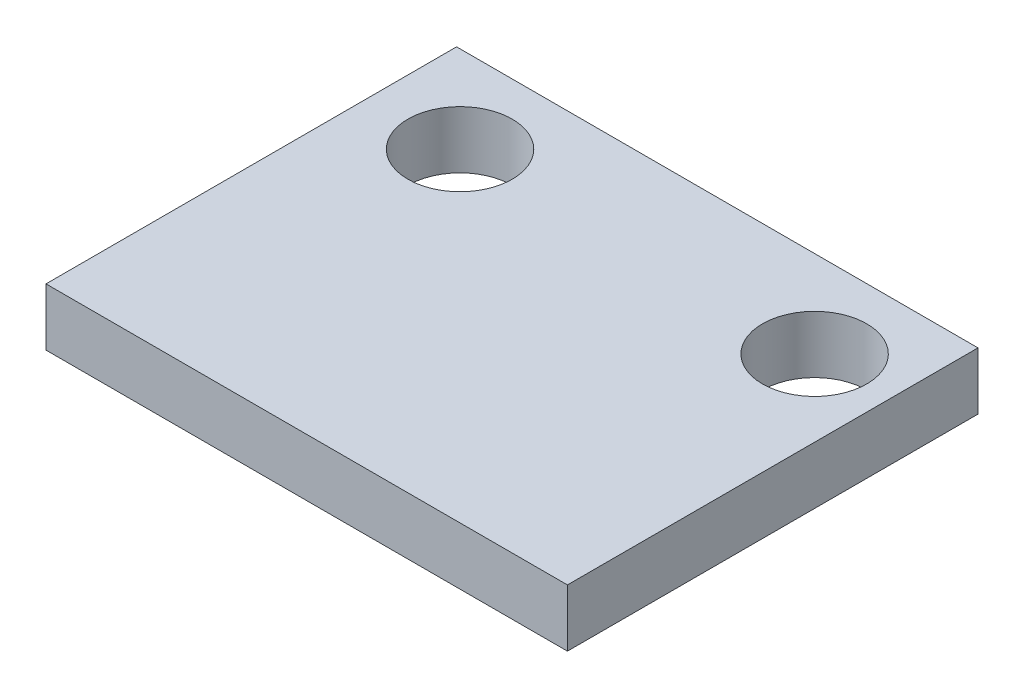
SolidWorks part; units mm, degrees
ref_plane "Front Plane" through (0, 0, 0) normal (0, 0, 1) x (1, 0, 0)
ref_plane "Top Plane" through (0, 0, 0) normal (0, 1, 0) x (1, 0, 0)
ref_plane "Right Plane" through (0, 0, 0) normal (1, 0, 0) x (0, 0, -1)
sketch "Sketch1" plane through (0, 0, 0) normal (0, 1, 0) x (1, 0, 0)
  line L1 (0, 0) -> (15, 0)
  line L2 (0, 0) -> (0, 11.811)
  line L3 (0, 11.811) -> (15, 11.811)
  line L4 (15, 0) -> (15, 11.811)
  circle A0 centre (2.6, 9.311) radius 1.5
  circle A1 centre (12.8, 9.311) radius 1.5
  point P11 (2.6, 10.811)
  point P12 (1.1, 9.311)
  point P13 (12.8, 10.811)
  point P14 (14.3, 9.311)
  dimension "D3" = 3
  dimension "D4" = 3
  dimension "D1" = 15
  dimension "D2" = 11.811
  dimension "D5" = 1.1
  dimension "D6" = 0.7
  dimension "D7" = 1
  dimension "D8" = 1
extrude "Boss-Extrude1" add sketch "Sketch1" along normal blind 1.651
